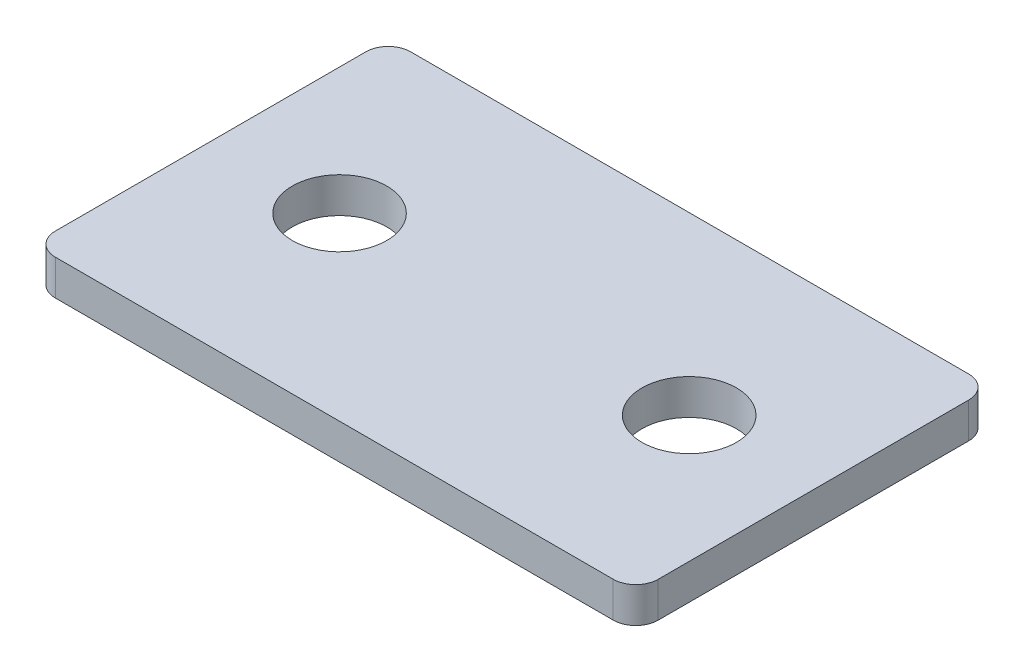
SolidWorks part; units mm, degrees
ref_plane "Front Plane" through (0, 0, 0) normal (0, 0, 1) x (1, 0, 0)
ref_plane "Top Plane" through (0, 0, 0) normal (0, 1, 0) x (1, 0, 0)
ref_plane "Right Plane" through (0, 0, 0) normal (1, 0, 0) x (0, 0, -1)
sketch "Sketch1" plane through (0, 0, 0) normal (0, 1, 0) x (1, 0, 0)
  line L0 (0, 10.033) -> (0, -10.033) construction
  line L1 (-15.748, 10.033) -> (15.748, 10.033)
  line L2 (-17.018, 8.763) -> (-17.018, -8.763)
  line L3 (-15.748, -10.033) -> (15.748, -10.033)
  line L4 (17.018, 8.763) -> (17.018, -8.763)
  line L5 (-17.018, 10.033) -> (17.018, -10.033) construction
  line L6 (-17.018, -10.033) -> (17.018, 10.033) construction
  circle A0 centre (-9.868, 0.133) radius 4.5 construction
  circle A1 centre (9.868, 0.133) radius 4.5 construction
  circle A2 centre (-9.868, 0.133) radius 2.667
  circle A3 centre (9.868, 0.133) radius 2.667
  arc A4 (-17.018, -8.763) -> (-15.748, -10.033) centre (-15.748, -8.763) ccw
  arc A5 (15.748, -10.033) -> (17.018, -8.763) centre (15.748, -8.763) ccw
  arc A6 (15.748, 10.033) -> (17.018, 8.763) centre (15.748, 8.763) cw
  arc A7 (-15.748, 10.033) -> (-17.018, 8.763) centre (-15.748, 8.763) ccw
  point P0 (0, 0)
  dimension "D3" = 9
  dimension "D5" = 2.65
  dimension "D6" = 5.334
  dimension "D7" = 1.27
  dimension "D1" = 20.066
  dimension "D2" = 34.036
  dimension "D4" = 5.4
extrude "Boss-Extrude1" add sketch "Sketch1" along normal blind 2
